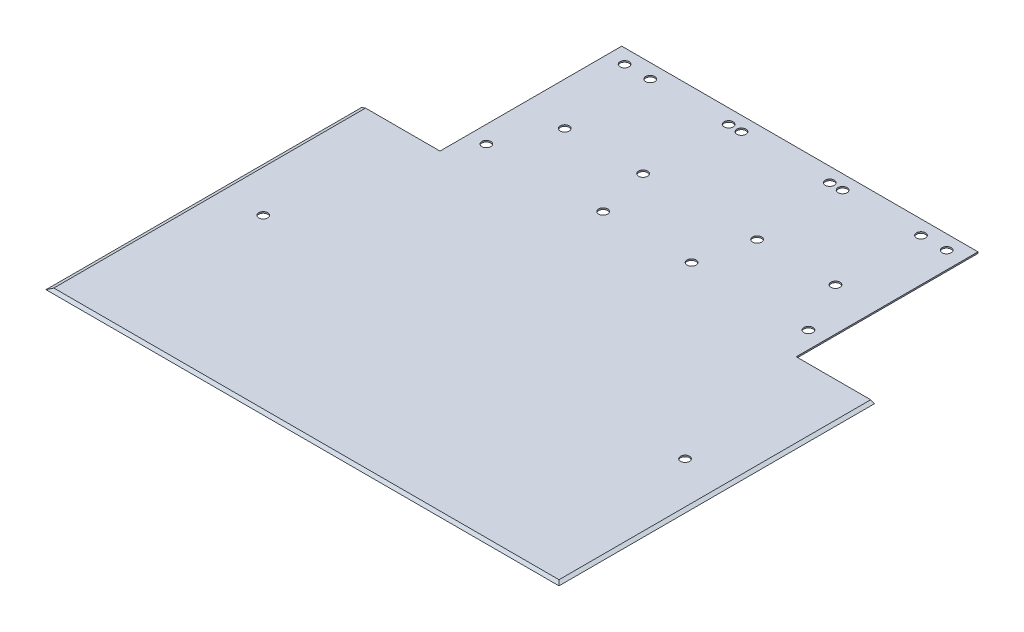
SolidWorks part; units mm, degrees
ref_plane "Alzado" through (0, 0, 0) normal (0, 0, 1) x (1, 0, 0)
ref_plane "Planta" through (0, 0, 0) normal (0, 1, 0) x (1, 0, 0)
ref_plane "Vista lateral" through (0, 0, 0) normal (1, 0, 0) x (0, 0, -1)
sketch "Croquis2" plane through (0, 0, 0) normal (0, 1, 0) x (1, 0, 0)
  line L0 (-90, 25.54) -> (-62.5, 25.54)
  line L1 (90, -85.2) -> (-90, -85.2)
  line L2 (90, -85.2) -> (90, 25.54)
  line L3 (62.5, 89.31) -> (-62.5, 89.31)
  line L4 (-90, -85.2) -> (-90, 25.54)
  line L5 (90, -85.2) -> (-62.5, 59.1667) construction
  line L6 (62.5, 59.1667) -> (-90, -85.2) construction
  line L7 (-62.5, 25.54) -> (-62.5, 89.31)
  line L8 (0, 4.11) -> (0, 89.31) construction
  line L9 (90, 25.54) -> (62.5, 25.54)
  line L10 (62.5, 25.54) -> (62.5, 89.31)
  point P0 (0, 0)
  dimension "D1" = 125
  dimension "D2" = 180
  dimension "D3" = 110.74
  dimension "D4" = 63.77
extrude "Saliente-Extruir1" add sketch "Croquis2" along normal blind 0.5
sketch "Croquis3" plane through (90, 0, 0) normal (1, 0, 0) x (0, 0, -1)
  line L0 (-85.2, 0) -> (-83.8263, 0.5)
  line L1 (-85.2, 0.5) -> (25.54, 0.5) construction
  line L2 (-83.8263, 0.5) -> (-85.2, 0.5)
  line L3 (-85.2, 0.5) -> (-85.2, 0)
  dimension "D1" = 70
sketch "Croquis5" plane through (0, 0.5, 0) normal (0, 1, 0) x (1, 0, 0)
  circle A0 centre (74, -24.9699) radius 1.585
sketch "Croquis6" plane through (0, 0.5, 0) normal (0, 1, 0) x (1, 0, 0)
  circle A0 centre (-56.5, 35.81) radius 1.585
  circle A1 centre (-15.5, 35.81) radius 1.585
  circle A2 centre (-15.5, 84.31) radius 1.585
  circle A3 centre (-56.5, 84.31) radius 1.585
extrude "Cortar-Extruir4" cut sketch "Croquis6" against normal up to next
sketch "Croquis7" plane through (0, 0.5, 0) normal (0, 1, 0) x (1, 0, 0)
  circle A0 centre (56.5, 35.81) radius 1.585
  circle A1 centre (15.5, 35.81) radius 1.585
  circle A2 centre (15.5, 84.31) radius 1.585
  circle A3 centre (56.5, 84.31) radius 1.585
extrude "Cortar-Extruir5" cut sketch "Croquis7" against normal up to next
mirror "Simetría3" about plane through (0, 0, 0) normal (1, 0, 0) of "Saliente-Extruir1"
sketch "Croquis8" plane through (0, 0.5, 0) normal (0, 1, 0) x (1, 0, 0)
  circle A0 centre (-20, 54.31) radius 1.585
  circle A1 centre (-47.5, 54.31) radius 1.585
  circle A2 centre (-47.5, 84.31) radius 1.585
  circle A3 centre (-20, 84.31) radius 1.585
extrude "Cortar-Extruir6" cut sketch "Croquis8" against normal up to next (0.5 mm away)
mirror "Simetría4" about plane through (0, 0, 0) normal (1, 0, 0) of "Cortar-Extruir6"
sketch "Croquis9" plane through (0, 0, 0) normal (0, -1, 0) x (1, 0, 0)
  circle A0 centre (56.5, -35.81) radius 1.585
  circle A2 centre (15.5, -35.81) radius 1.585
  circle A3 centre (15.5, -84.31) radius 1.585
  circle A4 centre (56.5, -84.31) radius 1.585
extrude "Cortar-Extruir7" cut sketch "Croquis9" against normal up to next (0.5 mm away)
mirror "Simetría5" about plane through (0, 0, 0) normal (1, 0, 0) of "Cortar-Extruir7"
extrude "Cortar-Extruir8" cut sketch "Croquis5" against normal up to next (0.5 mm away)
mirror "Simetría6" about plane through (0, 0, 0) normal (1, 0, 0) of "Cortar-Extruir8"
extrude "Cortar-Extruir9" cut sketch "Croquis3" against normal up to next
sketch "Croquis10" plane through (0, 0, -25.54) normal (0, 0, -1) x (-1, 0, 0)
  line L0 (90, 0) -> (90, 0.5)
  line L1 (90, 0.5) -> (88.6263, 0.5)
  line L2 (62.5, 0.5) -> (90, 0.5) construction
  line L3 (88.6263, 0.5) -> (90, 0)
  dimension "D1" = 70
extrude "Cortar-Extruir10" cut sketch "Croquis10" against normal up to next
mirror "Simetría7" about plane through (0, 0, 0) normal (1, 0, 0) of "Cortar-Extruir10"
